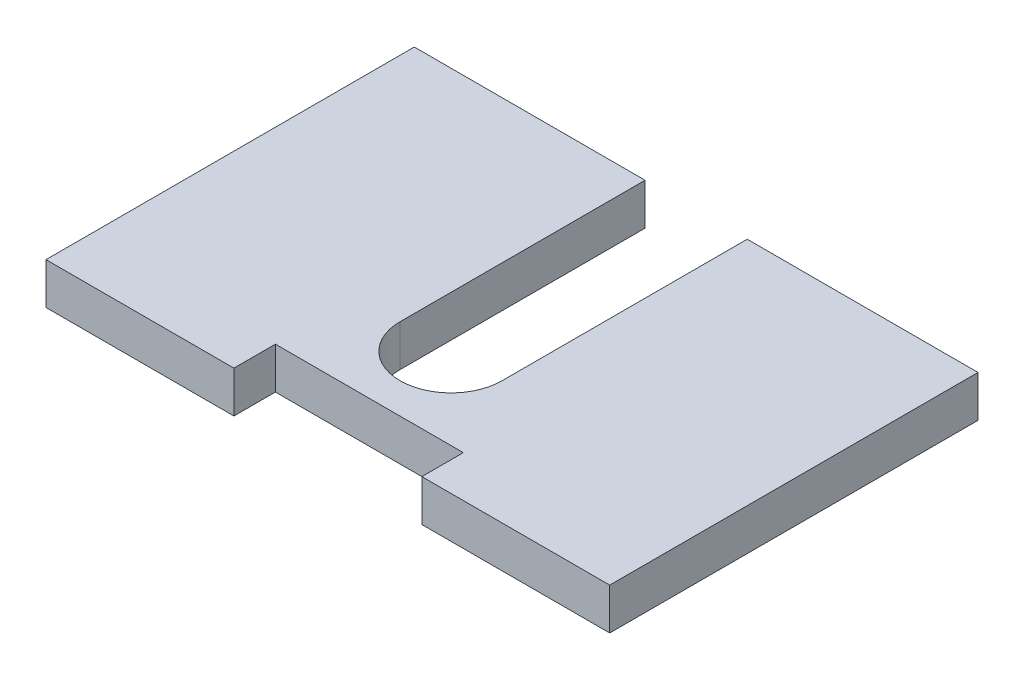
SolidWorks part; units mm, degrees
ref_plane "Front Plane" through (0, 0, 0) normal (0, 0, 1) x (1, 0, 0)
ref_plane "Top Plane" through (0, 0, 0) normal (0, 1, 0) x (1, 0, 0)
ref_plane "Right Plane" through (0, 0, 0) normal (1, 0, 0) x (0, 0, -1)
sketch "Sketch1" plane through (0, 0, 0) normal (0, 1, 0) x (1, 0, 0)
  line L1 (0, 0) -> (-69, 0)
  line L2 (0, 0) -> (0, 40)
  line L3 (0, 40) -> (-69, 40)
  line L4 (-69, 0) -> (-69, 40)
  dimension "D1" = 40
  dimension "D2" = 69
extrude "Boss-Extrude1" add sketch "Sketch1" along normal blind 5.08
sketch "Sketch2" plane through (0, 0, 0) normal (0, 0, 1) x (1, 0, 0)
  line L0 (-69, 0) -> (-46, 0) construction
  line L1 (-69, 0) -> (0, 0) construction
  line L2 (-46, 0) -> (-23, 0) construction
  line L3 (-23, 0) -> (0, 0) construction
  line L4 (-69, 5.08) -> (0, 5.08) construction
  line L5 (-69, 0) -> (-46, 0)
  line L6 (-69, 0) -> (-69, 5.08)
  line L7 (-69, 5.08) -> (-46, 5.08)
  line L8 (-46, 0) -> (-46, 5.08)
  line L10 (-23, 0) -> (0, 0)
  line L11 (-23, 0) -> (-23, 5.08)
  line L12 (-23, 5.08) -> (0, 5.08)
  line L13 (0, 0) -> (0, 5.08)
extrude "Boss-Extrude2" add sketch "Sketch2" along normal blind 5.08
sketch "Sketch7" plane through (0, 5.08, 0) normal (0, 1, 0) x (1, 0, 0)
  line L0 (-40.75, 10) -> (-40.75, 40) construction
  line L1 (0, 40) -> (-69, 40) construction
  line L2 (-28.25, 10) -> (-28.25, 40) construction
  line L3 (-34.5, 20) -> (-69, 20) construction
  line L4 (-69, 40) -> (-69, -5.08) construction
  line L6 (-40.75, 10) -> (-28.25, 10)
  line L7 (-40.75, 10) -> (-40.75, 40)
  line L8 (-40.75, 40) -> (-28.25, 40)
  line L9 (-28.25, 10) -> (-28.25, 40)
  circle A0 centre (-34.5, 20) radius 15.425 construction
  circle A1 centre (-34.5, 10) radius 6.25
  line M12 (0, 40) -> (-69, 40)
  dimension "D1" = 30.85
  dimension "D2" = 10
  dimension "D3" = 12.5
extrude "Cut-Extrude4" cut sketch "Sketch7" against normal blind 5.08 contours L6 A1 | L6 A1 | A1 L9 L7 M12
equation "\"MDFThickness\"= .2in"
equation "\"D1@Boss-Extrude1\"=\"MDFThickness\""
equation "\"D1@Boss-Extrude2\"=\"MDFThickness\""
equation "\"D1@Cut-Extrude4\"=\"MDFThickness\""
